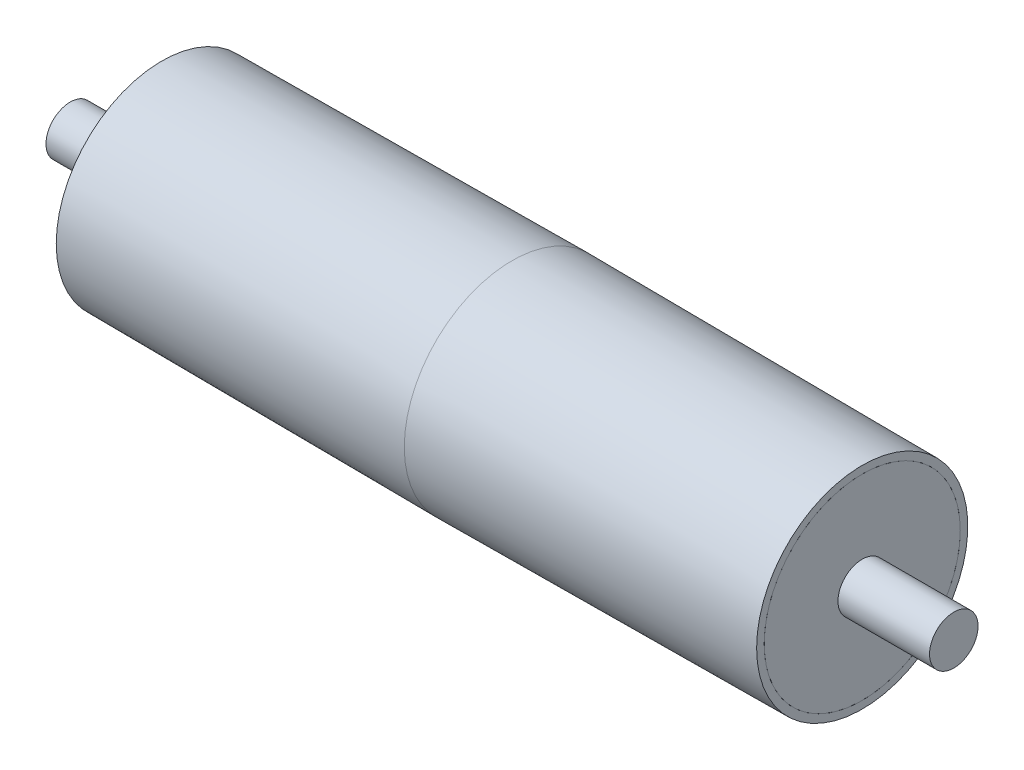
SolidWorks part; units mm, degrees
ref_plane "Front Plane" through (0, 0, 0) normal (0, 0, 1) x (1, 0, 0)
ref_plane "Top Plane" through (0, 0, 0) normal (0, 1, 0) x (1, 0, 0)
ref_plane "Right Plane" through (0, 0, 0) normal (1, 0, 0) x (0, 0, -1)
sketch "Sketch1" plane through (0, 0, 0) normal (0, 0, 1) x (1, 0, 0)
  line L0 (-325, 98) -> (325, 98) construction
  line L1 (-325, 98) -> (0, 100)
  line L2 (0, 0) -> (0, 98) construction
  line L3 (325, 98) -> (0, 100)
  line L4 (0, 0) -> (-22.4876, 0) construction
  line L5 (-325, 98) -> (-325, 0)
  line L6 (-325, 0) -> (325, 0)
  line L7 (325, 0) -> (325, 98)
  point P2 (0, 98)
  dimension "D1" = 2
  dimension "D2" = 650
  dimension "D3" = 100
revolve "Revolve1" add sketch "Sketch1" angle 360 about L6
shell "Shell1" thickness 7
sketch "Sketch2" plane through (325, 0, 0) normal (1, 0, 0) x (0, 0, -1)
  circle A0 centre (0, 0) radius 90.9999
  circle A1 centre (0, 0) radius 90.9999 construction
extrude "Boss-Extrude1" add sketch "Sketch2" against normal blind 10 separate body
mirror "Mirror2" about plane through (0, 0, 0) normal (1, 0, 0) of bodies 102
sketch "Sketch3" plane through (325, 0, 0) normal (1, 0, 0) x (0, 0, -1)
  circle A0 centre (0, 0) radius 22.5
  dimension "D1" = 45
extrude "Cut-Extrude1" cut sketch "Sketch3" against normal blind 735
sketch "Sketch4" plane through (0, 0, 0) normal (1, 0, 0) x (0, 0, -1)
  circle A0 centre (0, 0) radius 22.5
  circle A1 centre (0, 0) radius 22.5 construction
extrude "Boss-Extrude2" add sketch "Sketch4" along normal mid plane 820 separate body
sketch "Sketch5" plane through (0, 0, 0) normal (0, 1, 0) x (1, 0, 0)
  line L0 (347, 22.5) -> (347, 51.5814)
  line L1 (410, 22.5) -> (-410, 22.5) construction
  line L2 (347, 51.5814) -> (437.5433, 51.5814)
  line L3 (437.5433, 51.5814) -> (437.5433, 20)
  line L4 (437.5433, 20) -> (347, 20)
  line L5 (347, 20) -> (347, 22.5)
  line L6 (325, -98) -> (325, 98) construction
  line L7 (325, 0) -> (410, 0) construction
  line L8 (410, -22.5) -> (410, 22.5) construction
  dimension "D1" = 22
  dimension "D2" = 20
sketch "Sketch6" plane through (410, 0, 0) normal (1, 0, 0) x (0, 0, -1)
  circle A0 centre (0, 0) radius 20
  dimension "D1" = 40
